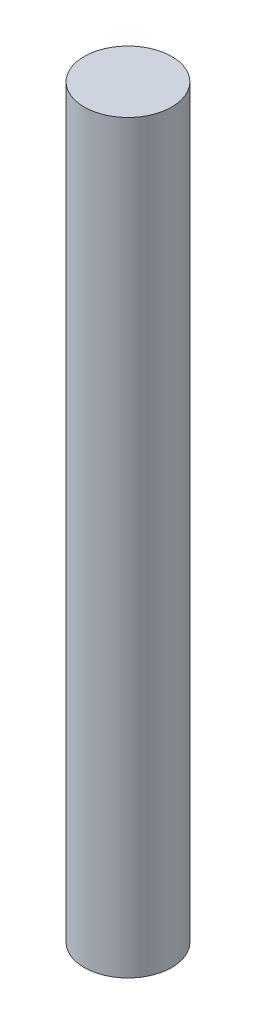
SolidWorks part; units mm, degrees
ref_plane "Front Plane" through (0, 0, 0) normal (0, 0, 1) x (1, 0, 0)
ref_plane "Top Plane" through (0, 0, 0) normal (0, 1, 0) x (1, 0, 0)
ref_plane "Right Plane" through (0, 0, 0) normal (1, 0, 0) x (0, 0, -1)
sketch "Sketch1" plane through (0, 0, 0) normal (0, 1, 0) x (1, 0, 0)
  line L0 (-1.5, 2.1114) -> (1.5, 2.1114)
  circle A0 centre (0, 0) radius 5.875
  arc A1 (-1.5, 2.1114) -> (1.5, 2.1114) centre (0, 0) ccw
  dimension "D1" = 11.75
  dimension "D2" = 5.18
  dimension "D3" = 3
extrude "Boss-Extrude2" add sketch "Sketch1" along normal blind 20
sketch "Sketch2" plane through (0, 20, 0) normal (0, 1, 0) x (1, 0, 0)
  circle A0 centre (0, 0) radius 5.875
  dimension "D1" = 11.75
extrude "Boss-Extrude3" add sketch "Sketch2" along normal blind 80
